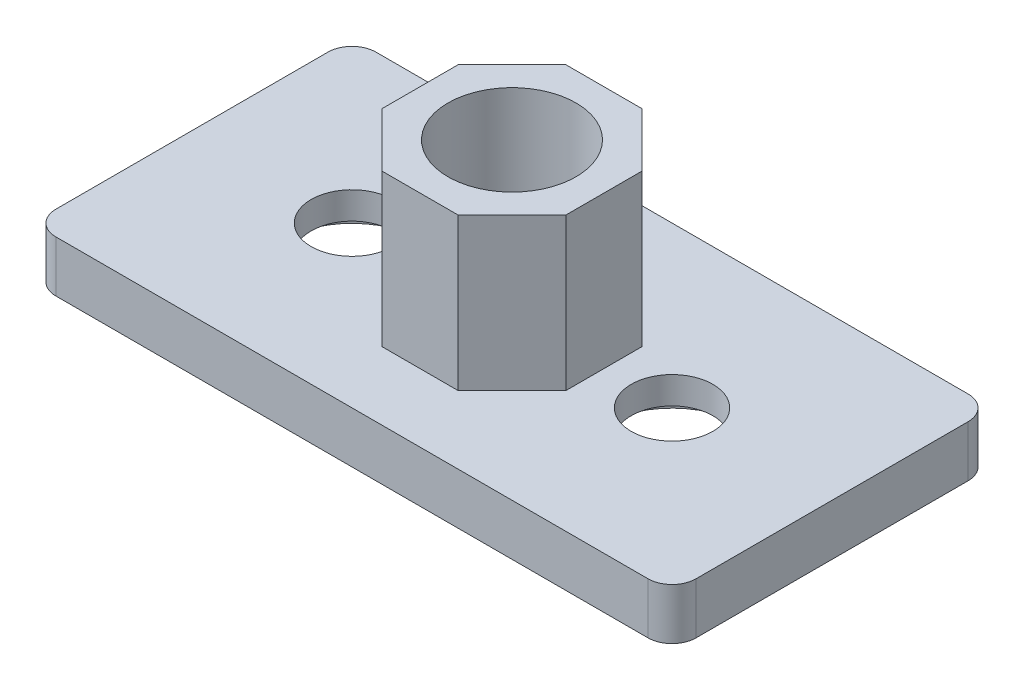
SolidWorks part; units mm, degrees
material "Delrin 2700 NC010, Low Viscosity Acetal Copolymer (SS)"
ref_plane "Front Plane" through (0, 0, 0) normal (0, 0, 1) x (1, 0, 0)
ref_plane "Top Plane" through (0, 0, 0) normal (0, 1, 0) x (1, 0, 0)
ref_plane "Right Plane" through (0, 0, 0) normal (1, 0, 0) x (0, 0, -1)
sketch "Sketch1" plane through (0, 0, 0) normal (0, 0, 1) x (1, 0, 0)
  line L1 (20, -1.6) -> (-20, -1.6)
  line L2 (20, -1.6) -> (20, 1.6)
  line L3 (20, 1.6) -> (-20, 1.6)
  line L4 (-20, -1.6) -> (-20, 1.6)
  line L5 (20, -1.6) -> (-20, 1.6) construction
  line L6 (20, 1.6) -> (-20, -1.6) construction
  point P0 (0, 0)
  dimension "D1" = 3.2
  dimension "D2" = 40
extrude "Boss-Extrude1" add sketch "Sketch1" along normal blind 20
sketch "Sketch3" plane through (0, 1.6, 0) normal (0, 1, 0) x (1, 0, 0)
  line L0 (-20, -10) -> (0, -10) construction
  line L1 (0, -10) -> (0, 0) construction
  line L2 (-20, -20) -> (-20, 0) construction
  circle A0 centre (-10, -10) radius 2.55
  circle A1 centre (10, -10) radius 2.55
  dimension "D1" = 5.1
  dimension "D2" = 20
extrude "Cut-Extrude2" cut sketch "Sketch3" against normal through all
sketch "Sketch5" plane through (0, -1.6, 0) normal (0, -1, 0) x (1, 0, 0)
  circle A0 centre (10, 10) radius 4.5
  circle A1 centre (-10, 10) radius 4.5
  dimension "D1" = 9
extrude "Cut-Extrude4" cut sketch "Sketch5" against normal blind 1.5
sketch "Sketch6" plane through (0, 1.6, 0) normal (0, 1, 0) x (1, 0, 0)
  line L0 (-20, 0) -> (20, -20) construction
  line L2 (-2.3817, -4.25) -> (-5.75, -7.6183)
  line L3 (-5.75, -7.6183) -> (-5.75, -12.3817)
  line L4 (-5.75, -12.3817) -> (-2.3817, -15.75)
  line L5 (-2.3817, -15.75) -> (2.3817, -15.75)
  line L6 (2.3817, -15.75) -> (5.75, -12.3817)
  line L7 (5.75, -12.3817) -> (5.75, -7.6183)
  line L8 (5.75, -7.6183) -> (2.3817, -4.25)
  line L9 (2.3817, -4.25) -> (-2.3817, -4.25)
  circle A0 centre (0, -10) radius 5.75 construction
  dimension "D1" = 11.5
extrude "Boss-Extrude2" add sketch "Sketch6" along normal blind 9.5
sketch "Sketch7" plane through (0, 11.1, 0) normal (0, 1, 0) x (1, 0, 0)
  line L0 (-5.75, -10) -> (5.75, -10) construction
  line L1 (-5.75, -7.6183) -> (-5.75, -12.3817) construction
  line L2 (5.75, -12.3817) -> (5.75, -7.6183) construction
  circle A0 centre (0, -10) radius 4
  dimension "D1" = 8
extrude "Cut-Extrude5" cut sketch "Sketch7" against normal through all
fillet "Fillet1" radius 1.5 4 edges at (20, 0, 0) (20, 0, 20) (-20, 0, 0) (-20, 0, 20)
